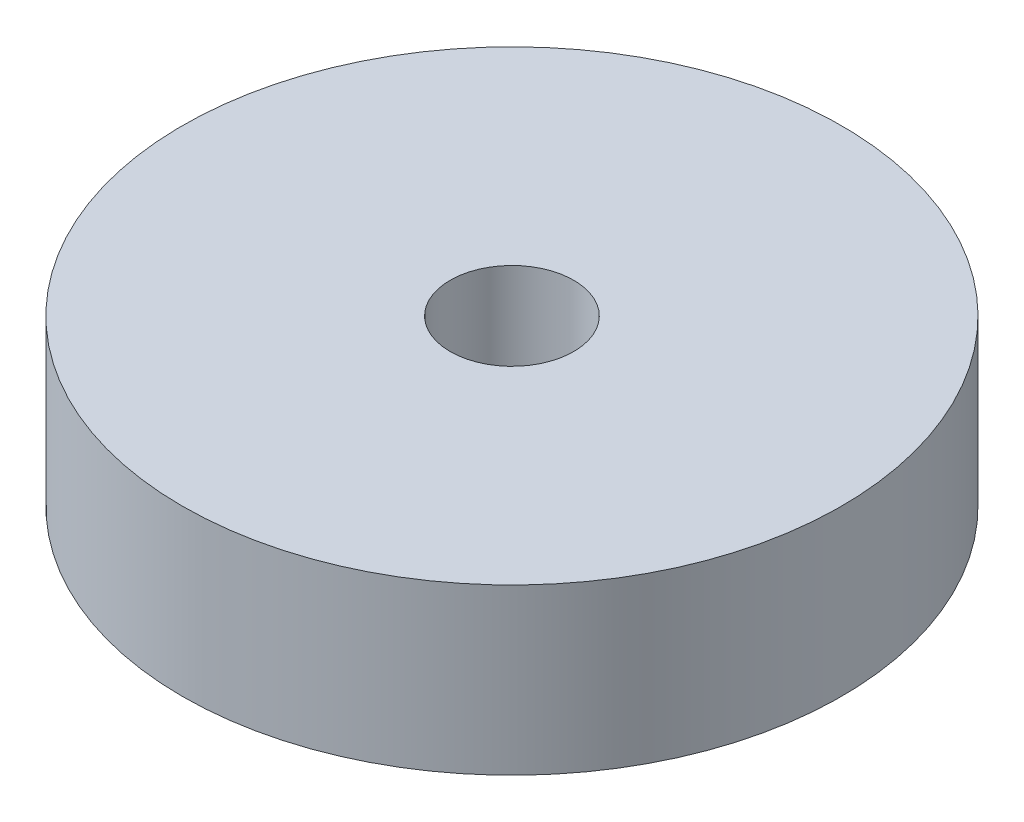
SolidWorks part; units mm, degrees
ref_plane "Front Plane" through (0, 0, 0) normal (0, 0, 1) x (1, 0, 0)
ref_plane "Top Plane" through (0, 0, 0) normal (0, 1, 0) x (1, 0, 0)
ref_plane "Right Plane" through (0, 0, 0) normal (1, 0, 0) x (0, 0, -1)
sketch "Sketch1" plane through (0, 0, 0) normal (0, 1, 0) x (1, 0, 0)
  line L0 (0, -171.7657) -> (0, 8416.5203) construction
  line L1 (-171.7657, 0) -> (8416.5203, 0) construction
  circle A0 centre (0, 0) radius 20
  dimension "D1" = 40
extrude "Boss-Extrude1" add sketch "Sketch1" along normal blind 10
sketch "Sketch2" plane through (0, 10, 0) normal (0, 1, 0) x (1, 0, 0)
  circle A0 centre (0, 0) radius 3.75
  dimension "D1" = 7.5
extrude "Cut-Extrude1" cut sketch "Sketch2" against normal through all both and the other way through all
